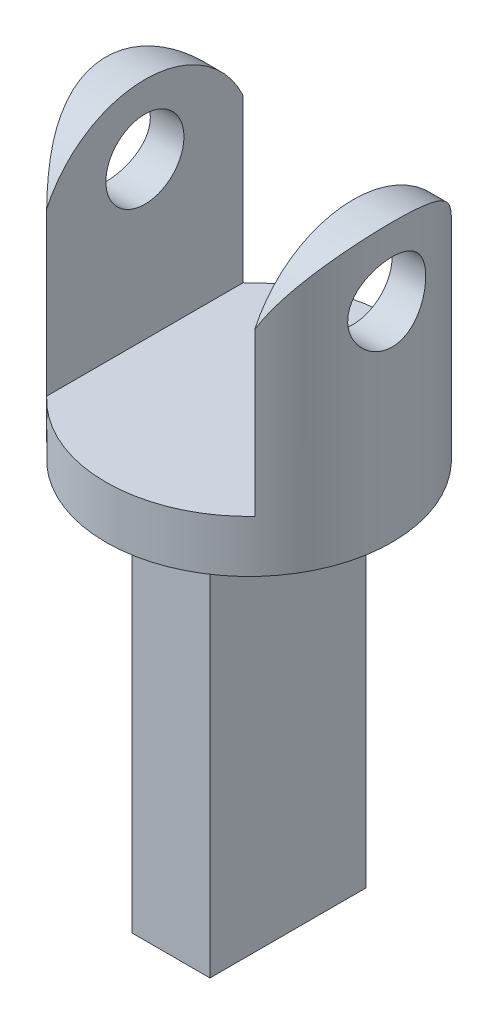
SolidWorks part; units mm, degrees
ref_plane "前视基准面" through (0, 0, 0) normal (0, 0, 1) x (1, 0, 0)
ref_plane "上视基准面" through (0, 0, 0) normal (0, 1, 0) x (1, 0, 0)
ref_plane "右视基准面" through (0, 0, 0) normal (1, 0, 0) x (0, 0, -1)
sketch "草图1" plane through (0, 0, 0) normal (0, 1, 0) x (1, 0, 0)
  circle A0 centre (0, 0) radius 5.5
  dimension "D1" = 11
extrude "凸台-拉伸1" add sketch "草图1" along normal blind 26
sketch "草图2" plane through (0, 0, 0) normal (0, 0, 1) x (1, 0, 0)
  line L0 (5.5, 26) -> (-5.5, 26) construction
  line L1 (-4, 35) -> (4, 35)
  line L2 (-4, 35) -> (-4, 17)
  line L3 (-4, 17) -> (4, 17)
  line L4 (4, 35) -> (4, 17)
  line L5 (-4, 35) -> (4, 17) construction
  line L6 (-4, 17) -> (4, 35) construction
  line L7 (5.5, 0) -> (5.5, 26) construction
  point P0 (0, 26)
  dimension "D1" = 9
  dimension "D2" = 1.5
extrude "切除-拉伸1" cut sketch "草图2" against normal mid plane 50
sketch "草图3" plane through (-4, 0, 0) normal (1, 0, 0) x (0, 0, -1)
  line L0 (3.7749, 26) -> (-3.7749, 26) construction
  circle A0 centre (0, 23) radius 1.5
  dimension "D1" = 3
  dimension "D2" = 3
extrude "切除-拉伸2" cut sketch "草图3" against normal mid plane 50
sketch "草图5" plane through (0, 0, 0) normal (1, 0, 0) x (0, 0, -1)
  line L1 (-4.1533, 21.5) -> (-12.2151, 24.9183)
  line L2 (-12.2151, 24.9183) -> (0.6299, 32.7807)
  line L3 (0.6299, 32.7807) -> (12.9914, 24.5987)
  line L4 (12.9914, 24.5987) -> (4.1533, 21.5)
  arc A0 (4.1533, 21.5) -> (-4.1533, 21.5) centre (0, 21.5) ccw
  circle A1 centre (0, 23) radius 1.5 construction
extrude "切除-拉伸3" cut sketch "草图5" against normal mid plane 22
sketch "草图6" plane through (0, 0, 0) normal (0, -1, 0) x (-1, 0, 0)
  line L1 (-12.9249, -13.0115) -> (12.9249, -13.0115)
  line L2 (-12.9249, -13.0115) -> (-12.9249, 13.0115)
  line L3 (-12.9249, 13.0115) -> (12.9249, 13.0115)
  line L4 (12.9249, -13.0115) -> (12.9249, 13.0115)
  line L5 (-12.9249, -13.0115) -> (12.9249, 13.0115) construction
  line L6 (-12.9249, 13.0115) -> (12.9249, -13.0115) construction
  line L7 (1.5, 3) -> (-1.5, 3)
  line L8 (1.5, 3) -> (1.5, -3)
  line L9 (1.5, -3) -> (-1.5, -3)
  line L10 (-1.5, 3) -> (-1.5, -3)
  line L11 (1.5, 3) -> (-1.5, -3) construction
  line L12 (1.5, -3) -> (-1.5, 3) construction
  point P0 (0, 0)
  point P6 (0, 0)
  dimension "D1" = 6
  dimension "D2" = 3
extrude "切除-拉伸4" cut sketch "草图6" against normal blind 15
